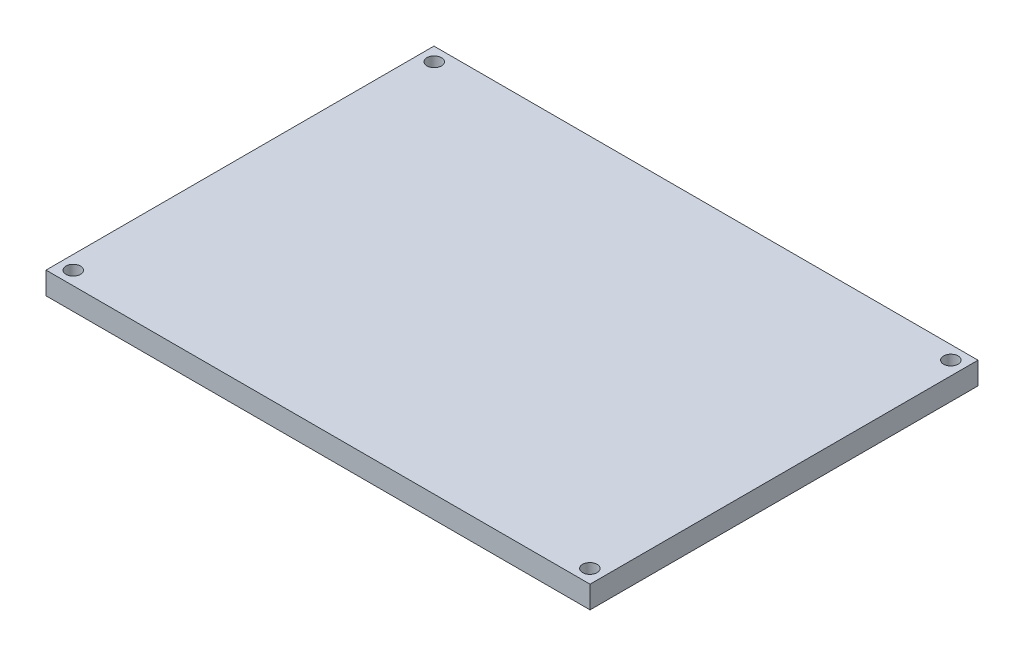
SolidWorks part; units mm, degrees
ref_plane "Front Plane" through (0, 0, 0) normal (0, 0, 1) x (1, 0, 0)
ref_plane "Top Plane" through (0, 0, 0) normal (0, 1, 0) x (1, 0, 0)
ref_plane "Right Plane" through (0, 0, 0) normal (1, 0, 0) x (0, 0, -1)
sketch "Sketch1" plane through (0, 0, 0) normal (0, 1, 0) x (1, 0, 0)
  line L0 (-1000, 0) -> (49000, 0) construction
  line L1 (-61, -43.5) -> (61, -43.5)
  line L2 (-61, -43.5) -> (-61, 43.5)
  line L3 (-61, 43.5) -> (61, 43.5)
  line L4 (61, -43.5) -> (61, 43.5)
  line L5 (-61, -43.5) -> (61, 43.5) construction
  line L6 (-61, 43.5) -> (61, -43.5) construction
  line L7 (0, -1000) -> (0, 49000) construction
  circle A0 centre (57.925, 40.475) radius 1.625
  circle A1 centre (-57.925, 40.475) radius 1.625
  circle A2 centre (-57.925, -40.475) radius 1.625
  circle A3 centre (57.925, -40.475) radius 1.625
  point P0 (0, 0)
  point P12 (0, 0)
  dimension "D3" = 3.25
  dimension "D5" = 3.025
  dimension "D1" = 122
  dimension "D2" = 87
  dimension "D4" = 3.075
extrude "Boss-Extrude1" add sketch "Sketch1" along normal blind 5
